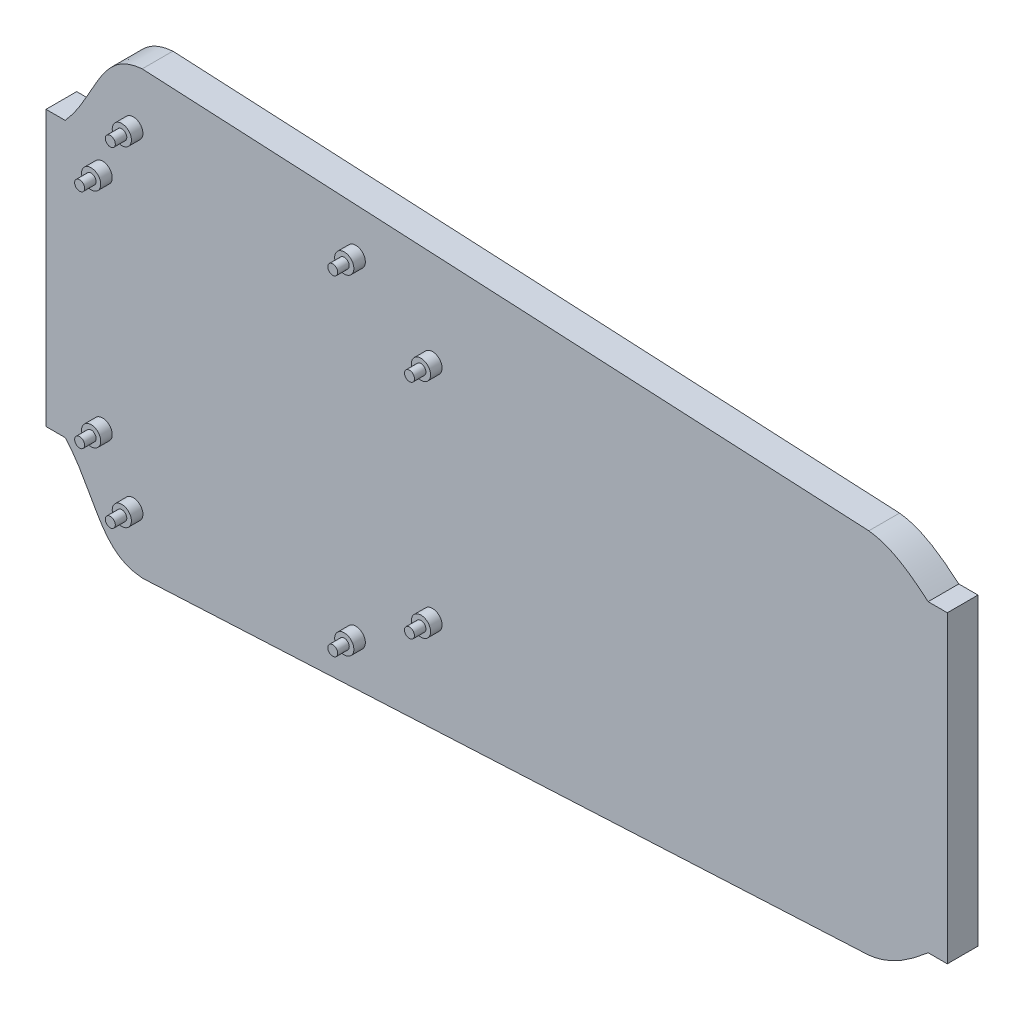
SolidWorks part; units mm, degrees
ref_plane "Front Plane" through (0, 0, 0) normal (0, 0, 1) x (1, 0, 0)
ref_plane "Top Plane" through (0, 0, 0) normal (0, 1, 0) x (1, 0, 0)
ref_plane "Right Plane" through (0, 0, 0) normal (1, 0, 0) x (0, 0, -1)
sketch "Sketch1" plane through (0, 0, 0) normal (0, 0, 1) x (1, 0, 0)
  line L0 (128.9591, 33.6286) -> (133.9591, 33.6286)
  line L1 (133.9591, 33.6286) -> (133.9591, -45.6561)
  line L2 (133.9591, -45.6561) -> (128.9591, -45.6561)
  line L3 (-96.0409, -41.8293) -> (-101.0409, -41.8293)
  line L4 (-101.0409, -41.8293) -> (-101.0409, 29.8017)
  line L5 (-101.0409, 29.8017) -> (-96.0409, 29.8017)
  line L41 (-75.9633, -63.5034) -> (113.4966, -53.9275)
  line L45 (113.4966, 41.9) -> (-75.9633, 51.476)
  spline S20 degree 3 poles (-96.0409, -41.8293) (-95.7989, -42.0932) (-95.562, -42.3621) (-94.0395, -44.1568) (-92.9236, -45.7924) (-90.8585, -49.1709) (-89.9111, -50.915) (-88.4578, -53.5103) (-87.9675, -54.372) (-86.9409, -56.0639) (-86.4049, -56.8943) (-85.5307, -58.0913) (-85.2274, -58.4821) (-84.5888, -59.2416) (-84.2542, -59.6091) (-83.2049, -60.6516) (-82.4406, -61.2706) (-81.1606, -62.0427) (-80.7193, -62.2694) (-79.8173, -62.6609) (-79.3554, -62.8265) (-77.9405, -63.2433) (-76.9542, -63.4142) (-75.9633, -63.5034) knots 0.352672 0.352672 0.352672 0.352672 0.375 0.375 0.5 0.5 0.625 0.625 0.6875 0.6875 0.75 0.75 0.78125 0.78125 0.8125 0.8125 0.875 0.875 0.90625 0.90625 0.9375 0.9375 1 1 1 1
  spline S21 degree 3 poles (113.4966, -53.9275) (114.9739, -53.7603) (116.3895, -53.4083) (118.4389, -52.6587) (119.1098, -52.372) (120.4306, -51.7359) (121.0829, -51.3848) (122.9889, -50.2675) (124.1972, -49.4372) (126.5417, -47.6779) (127.6776, -46.7485) (128.8505, -45.7489) (128.9048, -45.7025) (128.9591, -45.6561) knots 0 0 0 0 0.125 0.125 0.1875 0.1875 0.25 0.25 0.375 0.375 0.5 0.5 0.506074 0.506074 0.506074 0.506074
  spline S22 degree 3 poles (128.9591, 33.6286) (128.9134, 33.6677) (127.7512, 34.6604) (126.5688, 35.629) (124.8053, 36.9539) (124.207, 37.3838) (122.9921, 38.2061) (122.3746, 38.5993) (120.4843, 39.7099) (119.1742, 40.3597) (117.0932, 41.1246) (116.3871, 41.3415) (114.9575, 41.6873) (114.2325, 41.8167) (113.4966, 41.9) knots 0.494879 0.494879 0.494879 0.494879 0.5 0.625 0.625 0.6875 0.6875 0.75 0.75 0.875 0.875 0.9375 0.9375 1 1 1 1
  spline S23 degree 3 poles (-75.9633, 51.476) (-76.9698, 51.3853) (-77.9567, 51.2137) (-79.3959, 50.7857) (-79.8697, 50.6139) (-80.7968, 50.2046) (-81.2406, 49.9713) (-82.0898, 49.4495) (-82.4952, 49.1609) (-83.2715, 48.5337) (-83.643, 48.1944) (-84.7084, 47.1168) (-85.3332, 46.3434) (-86.4913, 44.7377) (-87.0238, 43.9049) (-88.0449, 42.211) (-88.533, 41.3497) (-89.9829, 38.7563) (-90.9324, 37.0136) (-92.9995, 33.6504) (-94.1146, 32.0312) (-95.6034, 30.2877) (-95.8197, 30.0429) (-96.0409, 29.8017) knots 0 0 0 0 0.0625 0.0625 0.09375 0.09375 0.125 0.125 0.15625 0.15625 0.1875 0.1875 0.25 0.25 0.3125 0.3125 0.375 0.375 0.5 0.5 0.625 0.625 0.645749 0.645749 0.645749 0.645749
  dimension "D2" = 5
  dimension "D1" = 5
extrude "Boss-Extrude1" add sketch "Sketch1" along normal blind 8
sketch "Sketch2" plane through (0, 0, 8) normal (0, 0, 1) x (1, 0, 0)
  line L0 (-101.0409, 29.8017) -> (-101.0409, -41.8293) construction
  line L1 (-101.0409, -6.0138) -> (133.9591, -6.0137)
  line L2 (133.9591, -45.6561) -> (133.9591, 33.6286) construction
  line L3 (16.4591, 46.8046) -> (16.4591, -58.8321)
  line L4 (113.4966, 41.9) -> (-75.9633, 51.476) construction
  line L5 (-75.9633, -63.5034) -> (113.4966, -53.9275) construction
  circle A0 centre (-86.2739, 22.9862) radius 2.5
  circle A1 centre (-78.2739, 36.9862) radius 2.5
  circle A2 centre (-20.2739, 36.9862) radius 2.5
  circle A3 centre (-0.2739, 22.9862) radius 2.5
  circle A4 centre (-0.2739, -35.0138) radius 2.5
  circle A5 centre (-20.2739, -49.0138) radius 2.5
  circle A6 centre (-78.2739, -49.0138) radius 2.5
  circle A7 centre (-86.2739, -35.0138) radius 2.5
  dimension "D5" = 5
  dimension "D4" = 5
  dimension "D1" = 117.5
  dimension "D2" = 58
  dimension "D3" = 86
extrude "Boss-Extrude2" add sketch "Sketch2" along normal blind 3 contours A5 | A4 | A6 | A7 | A0 | A1 | A2 | A3
sketch "Sketch3" plane through (0, 0, 11) normal (0, 0, 1) x (1, 0, 0)
  circle A0 centre (-86.2739, 22.9862) radius 1.3
  circle A1 centre (-78.2739, 36.9862) radius 1.3
  circle A2 centre (-20.2739, 36.9862) radius 1.3
  circle A3 centre (-0.2739, 22.9862) radius 1.3
  circle A4 centre (-0.2739, -35.0138) radius 1.3
  circle A5 centre (-20.2739, -49.0138) radius 1.3
  circle A6 centre (-78.2739, -49.0138) radius 1.3
  circle A7 centre (-86.2739, -35.0138) radius 1.3
  dimension "D1" = 2.6
  dimension "D2" = 2.6
  dimension "D3" = 2.6
  dimension "D4" = 2.6
extrude "Boss-Extrude3" add sketch "Sketch3" along normal blind 3 contours A6 | A5 | A4 | A7 | A0 | A1 | A3 | A2
